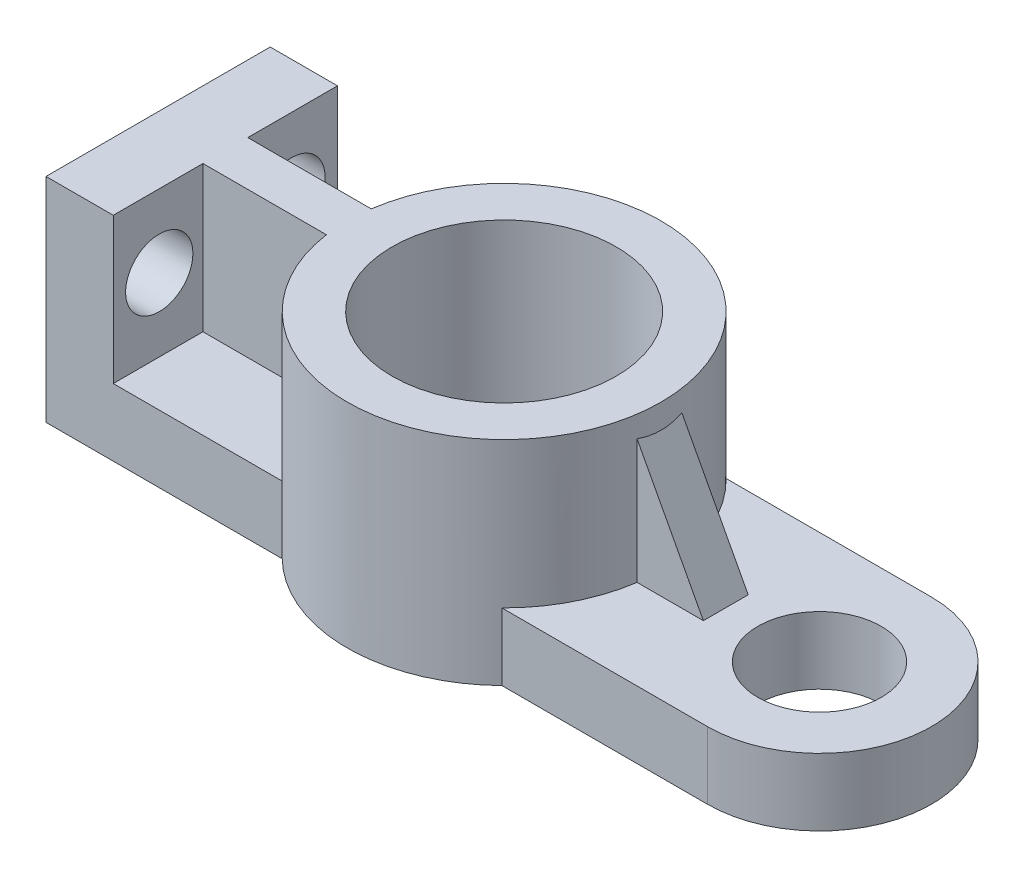
SolidWorks part; units mm, degrees
ref_plane "Front Plane" through (0, 0, 0) normal (0, 0, 1) x (1, 0, 0)
ref_plane "Top Plane" through (0, 0, 0) normal (0, 1, 0) x (1, 0, 0)
ref_plane "Right Plane" through (0, 0, 0) normal (1, 0, 0) x (0, 0, -1)
sketch "Sketch1" plane through (0, 0, 0) normal (0, 0, 1) x (1, 0, 0)
  line L0 (0, 80) -> (0, 0)
  line L1 (0, 0) -> (280, 0)
  point P2 (0, 0)
  dimension "D1" = 80
  dimension "D2" = 280
extrude "Extrude-Thin1" add sketch "Sketch1" along normal blind 100 thin contours L0 L1 thin type mid plane wall 30
sketch "Sketch2" plane through (280, 0, 0) normal (1, 0, 0) x (0, 0, -1)
  line L0 (-50, 15) -> (-50, -15)
  line L1 (-100, 15) -> (-50, 15)
  line L2 (-100, 15) -> (-100, -15)
  line L3 (-100, -15) -> (-50, -15)
revolve "Revolve1" add sketch "Sketch2" angle 180 about L0
sketch "Sketch3" plane through (0, 15, 0) normal (0, 1, 0) x (1, 0, 0)
  line L0 (280, 0) -> (280, -100) construction
  circle A0 centre (280, -50) radius 27.5
  dimension "D1" = 55
extrude "Cut-Extrude1" cut sketch "Sketch3" against normal through all and the other way through all
sketch "Sketch4" plane through (0, 15, 0) normal (0, 1, 0) x (1, 0, 0)
  line L0 (280, -50) -> (25.4474, -50) construction
  circle A0 centre (139.3427, -50) radius 70
  dimension "D1" = 140
extrude "Boss-Extrude1" add sketch "Sketch4" along normal blind 65 and the other way blind 30
sketch "Sketch5" plane through (0, 80, 0) normal (0, 1, 0) x (1, 0, 0)
  circle A0 centre (139.3427, -50) radius 50
  circle A1 centre (139.3427, -50) radius 70 construction
  dimension "D1" = 20
extrude "Cut-Extrude2" cut sketch "Sketch5" against normal through all
sketch "Sketch6" plane through (15, 0, 0) normal (1, 0, 0) x (0, 0, -1)
  line L0 (-79.4877, 47.5) -> (-79.4877, 15) construction
  line L1 (-100, 15) -> (0, 15) construction
  line L2 (-79.4877, 47.5) -> (-79.4877, 80) construction
  line L3 (-100, 80) -> (0, 80) construction
  line L4 (-50, 80) -> (-50, 15) construction
  circle A0 centre (-79.4877, 47.5) radius 15
  circle A1 centre (-20.5123, 47.5) radius 15
  dimension "D1" = 30
extrude "Cut-Extrude3" cut sketch "Sketch6" against normal through all
ref_plane "Plane1" through (0, 0, 50) normal (0, 0, 1) x (1, 0, 0)
sketch "Sketch8" plane through (0, 0, 50) normal (0, 0, 1) x (1, 0, 0)
  line L0 (15, 80) -> (69.3427, 80)
rib "Rib1" sketch "Sketch8" sketch "Sketch8" thickness 20 extrusion direction parallel to sketch draft on no parameters "D1"=20
sketch "Sketch14" plane through (0, 0, 50) normal (0, 0, 1) x (1, 0, 0)
  point P2 (206.4788, 80)
  point P3 (240.5839, 6.0619)
  point P4 (0, 0)
  point P5 (0, 0)
  point P6 (207.3914, 80)
  point P7 (209.3427, 80)
  point P8 (209.3427, 80)
  point P9 (209.3427, 80)
  point P10 (209.0976, 80)
  point P11 (0, 0)
  point P12 (208.9552, 80)
  point P15 (208.7242, 80)
  point P16 (208.1304, 80)
  point P17 (209.1432, 80)
  point P18 (208.8597, 80)
  point P19 (236.4824, 15)
sketch "Sketch15" plane through (0, 0, 50) normal (0, 0, 1) x (1, 0, 0)
  line L0 (203.5393, 80) -> (242.574, 6.7926)
  line L2 (209.3427, 80) -> (70.0606, 80) construction
  point P3 (242.574, 6.7926)
  point P5 (209.3427, 80)
  point P6 (203.5393, 80)
rib "Rib23" sketch "Sketch15" sketch "Sketch15" thickness 20 extrusion direction parallel to sketch draft on no parameters "D1"=20
